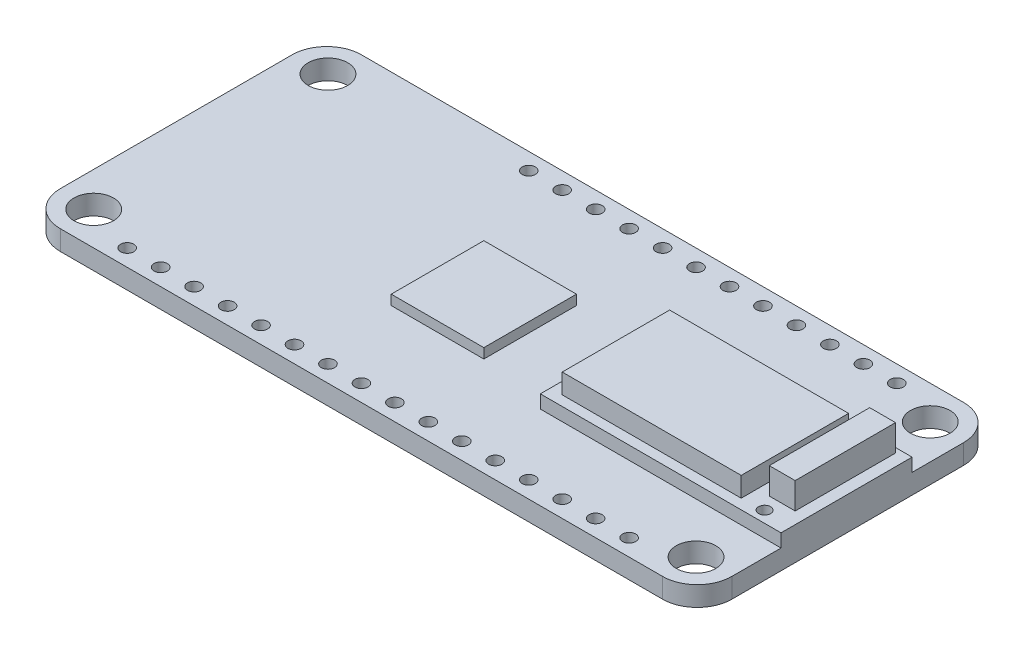
SolidWorks part; units mm, degrees
material "Brass"
ref_plane "Front Plane" through (0, 0, 0) normal (0, 0, 1) x (1, 0, 0)
ref_plane "Top Plane" through (0, 0, 0) normal (0, 1, 0) x (1, 0, 0)
ref_plane "Right Plane" through (0, 0, 0) normal (1, 0, 0) x (0, 0, -1)
sketch "Sketch1" plane through (0, 0, 0) normal (0, 1, 0) x (1, 0, 0)
  line L0 (16.6, -1.27) -> (44.54, -1.27) construction
  line L1 (2.63, 0) -> (48.35, 0)
  line L2 (0, -2.63) -> (0, -20.23)
  line L3 (2.63, -22.86) -> (48.35, -22.86)
  line L4 (50.98, -2.63) -> (50.98, -20.23)
  line L5 (44.54, -1.27) -> (44.54, -21.59) construction
  line L6 (44.54, -21.59) -> (6.44, -21.59) construction
  line L7 (2.63, -2.54) -> (48.35, -2.54) construction
  line L8 (48.35, -2.54) -> (48.35, -20.32) construction
  line L9 (48.35, -20.32) -> (2.63, -20.32) construction
  line L10 (6.44, -21.59) -> (8.98, -21.59) construction
  line L11 (44.54, -1.27) -> (42, -1.27) construction
  circle A0 centre (6.44, -21.59) radius 0.5
  circle A1 centre (8.98, -21.59) radius 0.5
  circle A2 centre (11.52, -21.59) radius 0.5
  circle A3 centre (14.06, -21.59) radius 0.5
  circle A4 centre (16.6, -21.59) radius 0.5
  circle A5 centre (19.14, -21.59) radius 0.5
  circle A6 centre (21.68, -21.59) radius 0.5
  circle A7 centre (24.22, -21.59) radius 0.5
  circle A8 centre (26.76, -21.59) radius 0.5
  circle A9 centre (29.3, -21.59) radius 0.5
  circle A10 centre (31.84, -21.59) radius 0.5
  circle A11 centre (34.38, -21.59) radius 0.5
  circle A12 centre (36.92, -21.59) radius 0.5
  circle A13 centre (39.46, -21.59) radius 0.5
  circle A14 centre (42, -21.59) radius 0.5
  circle A15 centre (44.54, -21.59) radius 0.5
  circle A16 centre (44.54, -1.27) radius 0.5
  circle A17 centre (42, -1.27) radius 0.5
  circle A18 centre (39.46, -1.27) radius 0.5
  circle A19 centre (36.92, -1.27) radius 0.5
  circle A20 centre (34.38, -1.27) radius 0.5
  circle A21 centre (31.84, -1.27) radius 0.5
  circle A22 centre (29.3, -1.27) radius 0.5
  circle A23 centre (26.76, -1.27) radius 0.5
  circle A24 centre (24.22, -1.27) radius 0.5
  circle A25 centre (21.68, -1.27) radius 0.5
  circle A26 centre (19.14, -1.27) radius 0.5
  circle A27 centre (16.6, -1.27) radius 0.5
  circle A28 centre (2.63, -2.54) radius 1.5
  circle A29 centre (2.63, -20.32) radius 1.5
  circle A30 centre (48.35, -20.32) radius 1.5
  circle A31 centre (48.35, -2.54) radius 1.5
  arc A32 (48.35, 0) -> (50.98, -2.63) centre (48.35, -2.63) cw
  arc A33 (48.35, -22.86) -> (50.98, -20.23) centre (48.35, -20.23) ccw
  arc A34 (0, -20.23) -> (2.63, -22.86) centre (2.63, -20.23) ccw
  arc A35 (2.63, 0) -> (0, -2.63) centre (2.63, -2.63) ccw
  point P80 (50.98, 0)
  point P85 (0, -22.86)
  point P88 (0, 0)
  dimension "D5" = 1
  dimension "D9" = 12
  dimension "D12" = 2.54
  dimension "D15" = 3
  dimension "D16" = 2.63
  dimension "D17" = 2.63
  dimension "D18" = 2.63
  dimension "D19" = 2.63
  dimension "D1" = 50.98
  dimension "D2" = 22.86
  dimension "D3" = 20.32
  dimension "D4" = 17.78
  dimension "D7" = 2.54
  dimension "D8" = 6.44
  dimension "D10" = 2.54
  dimension "D11" = 1.27
  dimension "D13" = 2.63
  dimension "D14" = 45.72
  dimension "D6" = 16
extrude "Boss-Extrude1" add sketch "Sketch1" along normal blind 1.5
sketch "Sketch2" [suppressed] plane through (0, 1.5, 0) normal (0, 1, 0) x (1, 0, 0)
  line L0 (6.94, -21.59) -> (6.94, 0) construction
  line L1 (48.35, 0) -> (2.63, 0) construction
  line L2 (9.48, -21.59) -> (9.48, 0) construction
  line L3 (12.02, -21.59) -> (12.02, 0) construction
  line L4 (14.56, -21.59) -> (14.56, 0) construction
  line L5 (17.1, -21.59) -> (17.1, -1.27) construction
  line L6 (19.64, -21.59) -> (19.64, -1.27) construction
  line L7 (22.18, -21.59) -> (22.18, -1.27) construction
  line L8 (24.72, -21.59) -> (24.72, -1.27) construction
  line L9 (27.26, -21.59) -> (27.26, -1.27) construction
  line L10 (29.8, -21.59) -> (29.8, -1.27) construction
  line L11 (32.34, -21.59) -> (32.34, -1.27) construction
  line L12 (34.88, -21.59) -> (34.88, -1.27) construction
  line L13 (37.42, -21.59) -> (37.42, -1.27) construction
  line L14 (39.96, -21.59) -> (39.96, -1.27) construction
  line L15 (42.5, -21.59) -> (42.5, -1.27) construction
  line L16 (45.04, -21.59) -> (45.04, -1.27) construction
  circle A0 centre (6.44, -21.59) radius 0.5 construction
  circle A1 centre (8.98, -21.59) radius 0.5 construction
  circle A2 centre (11.52, -21.59) radius 0.5 construction
  circle A3 centre (14.06, -21.59) radius 0.5 construction
  circle A4 centre (16.6, -21.59) radius 0.5 construction
  circle A5 centre (16.6, -1.27) radius 0.5 construction
  circle A6 centre (19.14, -21.59) radius 0.5 construction
  circle A7 centre (19.14, -1.27) radius 0.5 construction
  circle A8 centre (21.68, -21.59) radius 0.5 construction
  circle A9 centre (21.68, -1.27) radius 0.5 construction
  circle A10 centre (24.22, -21.59) radius 0.5 construction
  circle A11 centre (24.22, -1.27) radius 0.5 construction
  circle A12 centre (26.76, -21.59) radius 0.5 construction
  circle A13 centre (26.76, -1.27) radius 0.5 construction
  circle A14 centre (29.3, -21.59) radius 0.5 construction
  circle A15 centre (29.3, -1.27) radius 0.5 construction
  circle A16 centre (31.84, -21.59) radius 0.5 construction
  circle A17 centre (31.84, -1.27) radius 0.5 construction
  circle A18 centre (34.38, -21.59) radius 0.5 construction
  circle A19 centre (34.38, -1.27) radius 0.5 construction
  circle A20 centre (36.92, -21.59) radius 0.5 construction
  circle A21 centre (36.92, -1.27) radius 0.5 construction
  circle A22 centre (39.46, -21.59) radius 0.5 construction
  circle A23 centre (39.46, -1.27) radius 0.5 construction
  circle A24 centre (42, -21.59) radius 0.5 construction
  circle A25 centre (42, -1.27) radius 0.5 construction
  circle A26 centre (44.54, -21.59) radius 0.5 construction
  circle A27 centre (44.54, -1.27) radius 0.5 construction
  text T0 "<b>  RST</b>"
  text T1 "<b>  3V</b>"
  text T2 "  ARf"
  text T3 "  GND"
  text T4 "  A0"
  text T5 "BAT  "
  text T6 "  A1"
  text T7 "  A2"
  text T8 "  A3"
  text T9 "  A4"
  text T10 "  A5"
  text T11 "  SCK"
  text T12 "  MOSI"
  text T13 "  MISO"
  text T14 "  0 RX"
  text T15 "  1 TX"
  text T16 "  DFU"
  text T17 "En  "
  text T18 "USB  "
  text T19 "13  "
  text T20 "12  "
  text T21 "~11  "
  text T22 "~10  "
  text T23 "9~  "
  text T24 "6  "
  text T25 "~5  "
  text T26 "SCL  "
  text T27 "SDA  "
extrude "Cut-Extrude1" [suppressed] cut sketch "Sketch2" against normal blind 0.5
sketch "Sketch3" plane through (0, 1.5, 0) normal (0, 1, 0) x (1, 0, 0)
  line L1 (33.6069, -7.5832) -> (47.1923, -7.5832)
  line L2 (33.6069, -7.5832) -> (33.6069, -15.7345)
  line L3 (33.6069, -15.7345) -> (47.1923, -15.7345)
  line L4 (47.1923, -7.5832) -> (47.1923, -15.7345)
extrude "Boss-Extrude2" add sketch "Sketch3" along normal blind 2.5
sketch "Sketch4" plane through (0, 1.5, 0) normal (0, 1, 0) x (1, 0, 0)
  line L1 (48.1179, -6.9076) -> (50.0823, -6.9076)
  line L2 (48.1179, -6.9076) -> (48.1179, -14.5282)
  line L3 (48.1179, -14.5282) -> (50.0823, -14.5282)
  line L4 (50.0823, -6.9076) -> (50.0823, -14.5282)
extrude "Boss-Extrude3" add sketch "Sketch4" along normal blind 3
sketch "Sketch5" plane through (0, 1.5, 0) normal (0, 1, 0) x (1, 0, 0)
  line L0 (50.98, -20.23) -> (50.98, -2.63) construction
  line L1 (32.7101, -6.5478) -> (50.98, -6.5478)
  line L2 (32.7101, -6.5478) -> (32.7101, -16.4991)
  line L3 (32.7101, -16.4991) -> (50.98, -16.4991)
  line L4 (50.98, -6.5478) -> (50.98, -16.4991)
  circle A0 centre (48.8655, -15.6328) radius 0.4576
extrude "Boss-Extrude4" add sketch "Sketch5" along normal blind 1
sketch "Sketch6" plane through (0, 1.5, 0) normal (0, 1, 0) x (1, 0, 0)
  line L1 (20.2464, -8.3243) -> (27.2769, -8.3243)
  line L2 (20.2464, -8.3243) -> (20.2464, -15.3548)
  line L3 (20.2464, -15.3548) -> (27.2769, -15.3548)
  line L4 (27.2769, -8.3243) -> (27.2769, -15.3548)
extrude "Boss-Extrude5" add sketch "Sketch6" along normal blind 0.75
